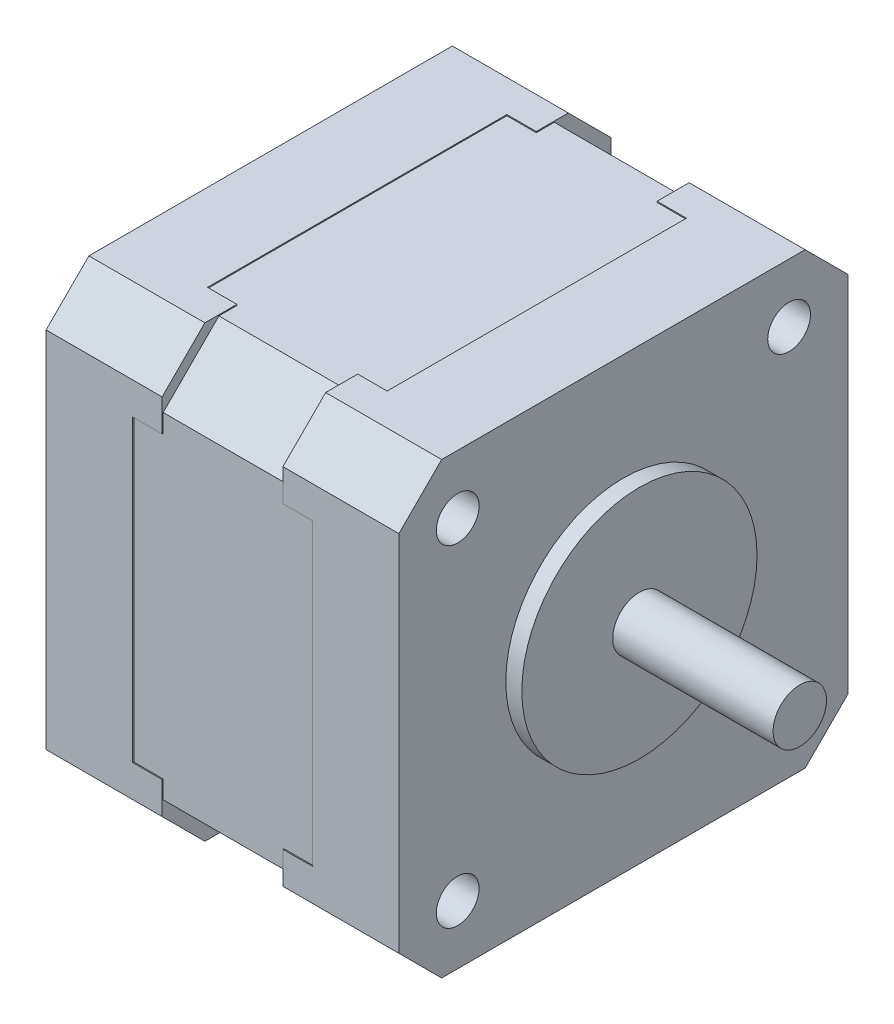
SolidWorks part; units mm, degrees
ref_plane "Alzado" through (0, 0, 0) normal (0, 0, 1) x (1, 0, 0)
ref_plane "Planta" through (0, 0, 0) normal (0, 1, 0) x (1, 0, 0)
ref_plane "Vista lateral" through (0, 0, 0) normal (1, 0, 0) x (0, 0, -1)
ref_plane "Plano1" through (-5.65, 0, 0) normal (-1, 0, 0) x (0, -1, 0)
sketch "Croquis1" plane through (-5.65, 0, 0) normal (-1, 0, 0) x (0, -1, 0)
  line L0 (20.9, -20.9) -> (20.9, 20.9)
  line L1 (20.9, 20.9) -> (-20.9, 20.9)
  line L2 (-20.9, 20.9) -> (-20.9, -20.9)
  line L3 (-20.9, -20.9) -> (20.9, -20.9)
extrude "Saliente-Extruir1" add sketch "Croquis1" against normal blind 11.3
sketch "Croquis2" plane through (5.65, 0, 0) normal (1, 0, 0) x (0, 0, -1)
  line L0 (21, 20.9) -> (21, -21)
  line L1 (21, -21) -> (-21, -21)
  line L2 (-21, -21) -> (-21, 20.9)
  line L3 (-21, 20.9) -> (21, 20.9)
extrude "Saliente-Extruir2" add sketch "Croquis2" along normal blind 10.85
sketch "Croquis3" plane through (0, 20.9, 0) normal (0, 1, 0) x (-1, 0, 0)
  line L0 (-5.65, -21) -> (-16.5, -21)
  line L1 (-16.5, -21) -> (-16.5, 21)
  line L2 (-16.5, 21) -> (-5.65, 21)
  line L3 (-5.65, 21) -> (-5.65, -21)
extrude "Saliente-Extruir3" add sketch "Croquis3" along normal blind 0.1
ref_plane "Plano2" through (-5.65, 0, 0) normal (1, 0, 0) x (0, 0, -1)
sketch "Croquis4" plane through (-5.65, 0, 0) normal (1, 0, 0) x (0, 0, -1)
  line L0 (21, 21) -> (-21, 21)
  line L1 (-21, 21) -> (-21, -21)
  line L2 (-21, -21) -> (21, -21)
  line L3 (21, -21) -> (21, 21)
extrude "Saliente-Extruir4" add sketch "Croquis4" against normal blind 10.85
ref_plane "Plano3" through (8.4, 0, 0) normal (1, 0, 0) x (0, 0, -1)
sketch "Croquis5" plane through (8.4, 0, 0) normal (1, 0, 0) x (0, 0, -1)
  line L0 (20.9, 14) -> (20.9, -14)
  line L1 (20.9, -14) -> (21, -14)
  line L2 (21, -14) -> (21, 14)
  line L3 (21, 14) -> (20.9, 14)
extrude "Cortar-Extruir1" cut sketch "Croquis5" against normal up to next
ref_plane "Plano4" through (-8.4, 0, 0) normal (-1, 0, 0) x (0, -1, 0)
sketch "Croquis6" plane through (-8.4, 0, 0) normal (-1, 0, 0) x (0, -1, 0)
  line L0 (-14, 21) -> (-14, 20.9)
  line L1 (-14, 20.9) -> (14, 20.9)
  line L2 (14, 20.9) -> (14, 21)
  line L3 (14, 21) -> (-14, 21)
extrude "Cortar-Extruir2" cut sketch "Croquis6" against normal up to next
sketch "Croquis7" plane through (0, -21, 0) normal (0, -1, 0) x (1, 0, 0)
  line L0 (8.4, -14) -> (8.4, 14)
  line L1 (8.4, 14) -> (5.65, 14)
  line L2 (5.65, 14) -> (5.65, -14)
  line L3 (5.65, -14) -> (8.4, -14)
extrude "Cortar-Extruir3" cut sketch "Croquis7" against normal blind 0.1
sketch "Croquis8" plane through (0, 0, 21) normal (0, 0, 1) x (1, 0, 0)
  line L0 (8.4, -14) -> (8.4, 14)
  line L1 (8.4, 14) -> (5.65, 14)
  line L2 (5.65, 14) -> (5.65, -14)
  line L3 (5.65, -14) -> (8.4, -14)
extrude "Cortar-Extruir4" cut sketch "Croquis8" against normal blind 0.1
sketch "Croquis9" plane through (5.65, 0, 0) normal (-1, 0, 0) x (0, 0, 1)
  line L0 (-14, 20.9) -> (14, 20.9)
  line L1 (14, 20.9) -> (14, 21)
  line L2 (14, 21) -> (-14, 21)
  line L3 (-14, 21) -> (-14, 20.9)
extrude "Cortar-Extruir5" cut sketch "Croquis9" against normal blind 2.75
sketch "Croquis10" plane through (0, -21, 0) normal (0, -1, 0) x (1, 0, 0)
  line L0 (-5.65, -14) -> (-5.65, 14)
  line L1 (-5.65, 14) -> (-8.4, 14)
  line L2 (-8.4, 14) -> (-8.4, -14)
  line L3 (-8.4, -14) -> (-5.65, -14)
extrude "Cortar-Extruir6" cut sketch "Croquis10" against normal blind 0.1
sketch "Croquis11" plane through (0, 0, -21) normal (0, 0, -1) x (-1, 0, 0)
  line L0 (5.65, 14) -> (5.65, -14)
  line L1 (5.65, -14) -> (8.4, -14)
  line L2 (8.4, -14) -> (8.4, 14)
  line L3 (8.4, 14) -> (5.65, 14)
extrude "Cortar-Extruir7" cut sketch "Croquis11" against normal blind 0.1
sketch "Croquis12" plane through (0, 21, 0) normal (0, 1, 0) x (-1, 0, 0)
  line L0 (5.65, 14) -> (5.65, -14)
  line L1 (5.65, -14) -> (8.4, -14)
  line L2 (8.4, -14) -> (8.4, 14)
  line L3 (8.4, 14) -> (5.65, 14)
extrude "Cortar-Extruir8" cut sketch "Croquis12" against normal blind 0.1
sketch "Croquis15" plane through (0, 0, 0) normal (0, 0, 1) x (1, 0, 0)
  line L0 (15.5, 11) -> (15.5, 0)
  line L1 (15.5, 0) -> (33, 0)
  line L2 (33, 0) -> (33, 2.5)
  line L3 (33, 2.5) -> (18, 2.5)
  line L4 (18, 2.5) -> (18, 11)
  line L5 (18, 11) -> (15.5, 11)
  line L6 (15.5, 0) -> (33, 0) construction
  dimension "D1" = 15
revolve "Revolución1" add sketch "Croquis15" angle 360 about L6
chamfer "Chaflán1" distance 5.2142 angle 45 4 edges at (0, -20.9, -20.9) (0, -20.9, 20.9)
chamfer "Chaflán2" distance 4 angle 45 8 edges at (-11.075, 21, -21) (-11.075, -21, 21) (11.075, -21, -21) (11.075, 21, -21) (-11.075, 21, 21) (11.075, 21, 21) (-11.075, -21, -21) (11.075, -21, 21)
ref_plane "Plano5" through (12.45, 0, 0) normal (1, 0, 0) x (0, 0, -1)
sketch "Croquis18" plane through (12.45, 0, 0) normal (1, 0, 0) x (0, 0, -1)
  line L0 (0, 0) -> (0, 2.3727) construction
  line L1 (0, 36.4567) -> (0, 0) construction
  line L2 (0, 0) -> (37.7341, 0) construction
  line L4 (15.5, -15.5) -> (-15.5, -15.5) construction
  line L5 (15.5, -15.5) -> (15.5, 15.5) construction
  line L6 (15.5, 15.5) -> (-15.5, 15.5) construction
  line L7 (-15.5, -15.5) -> (-15.5, 15.5) construction
  line L8 (15.5, -15.5) -> (-15.5, 15.5) construction
  line L9 (15.5, 15.5) -> (-15.5, -15.5) construction
  circle A0 centre (-15.5, 15.5) radius 2
  circle A1 centre (15.5, 15.5) radius 2
  circle A2 centre (15.5, -15.5) radius 2
  circle A3 centre (-15.5, -15.5) radius 2
  dimension "D3" = 4
  dimension "D1" = 15.5
  dimension "D2" = 15.5
extrude "Cortar-Extruir10" cut sketch "Croquis18" against normal blind 3 and the other way blind 6
